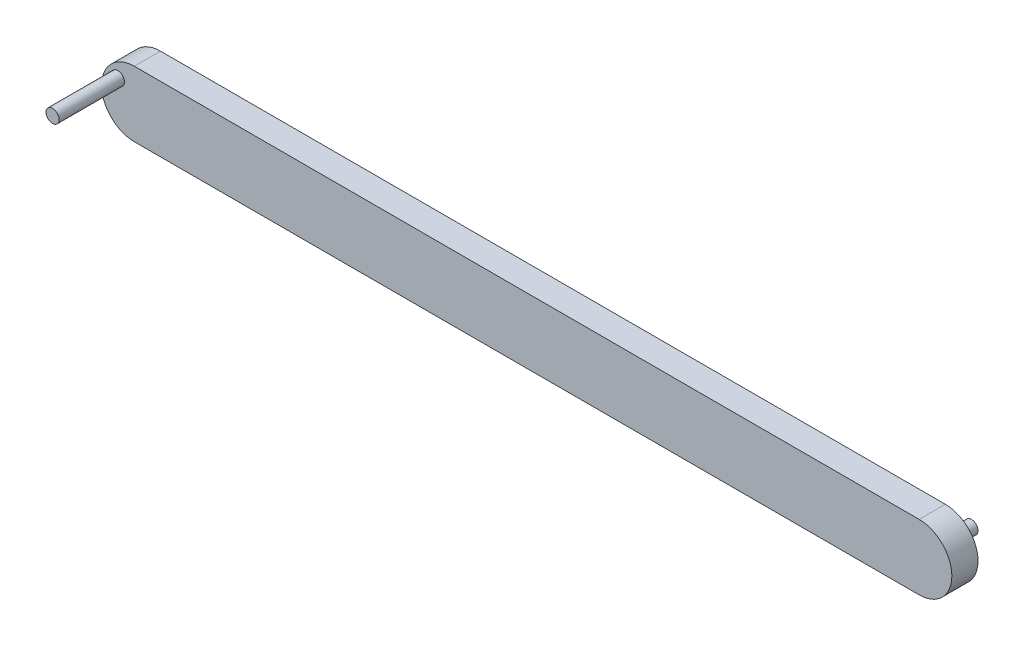
SolidWorks part; units mm, degrees
ref_plane "Front Plane" through (0, 0, 0) normal (0, 0, 1) x (1, 0, 0)
ref_plane "Top Plane" through (0, 0, 0) normal (0, 1, 0) x (1, 0, 0)
ref_plane "Right Plane" through (0, 0, 0) normal (1, 0, 0) x (0, 0, -1)
sketch "Sketch1" plane through (0, 0, 0) normal (0, 0, 1) x (1, 0, 0)
  line L0 (-30, 0) -> (30, 0)
  line L1 (-30, -5) -> (30, -5)
  arc A0 (-30, 0) -> (-30, -5) centre (-30, -2.5) ccw
  arc A1 (30, -5) -> (30, 0) centre (30, -2.5) ccw
  dimension "D1" = 60
  dimension "D2" = 30
  dimension "D3" = 5
extrude "Boss-Extrude1" add sketch "Sketch1" along normal blind 2
sketch "Sketch2" plane through (0, 0, 0) normal (0, 0, -1) x (-1, 0, 0)
  circle A0 centre (-30, -2.5) radius 0.5
  dimension "D1" = 1
extrude "Boss-Extrude2" add sketch "Sketch2" along normal blind 2
sketch "Sketch3" plane through (0, 0, 2) normal (0, 0, 1) x (1, 0, 0)
  circle A0 centre (-31.2514, -1.4137) radius 0.5
  dimension "D1" = 1
extrude "Boss-Extrude3" add sketch "Sketch3" along normal blind 5
